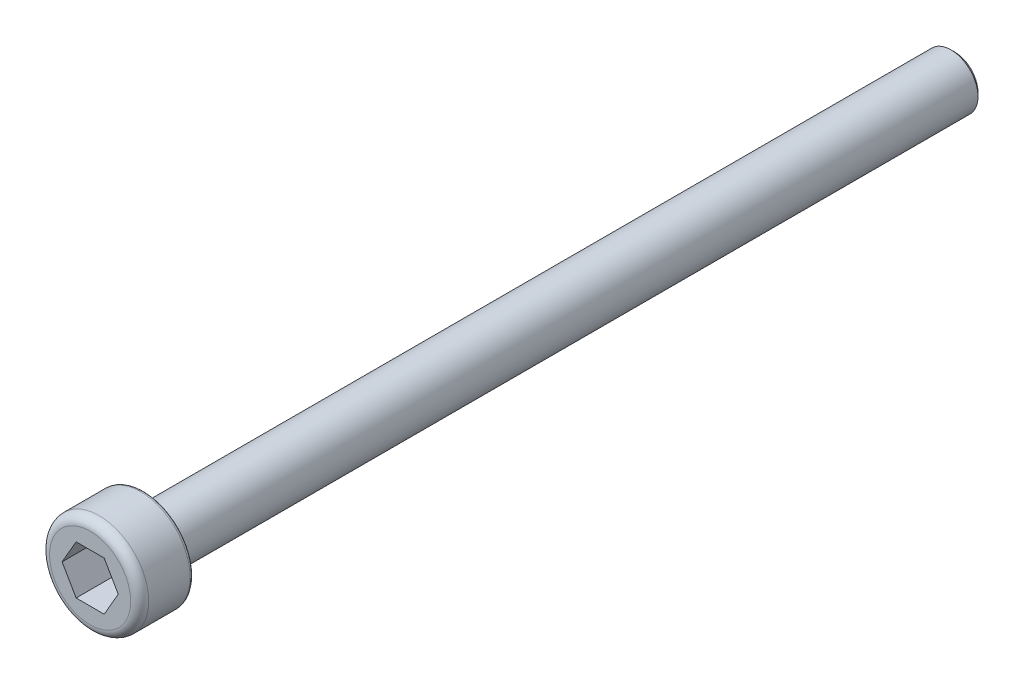
SolidWorks part; units mm, degrees
ref_plane "前视" through (0, 0, 0) normal (0, 0, 1) x (1, 0, 0)
ref_plane "上视" through (0, 0, 0) normal (0, 1, 0) x (1, 0, 0)
ref_plane "右视" through (0, 0, 0) normal (1, 0, 0) x (0, 0, -1)
sketch "草图1" plane through (0, 0, 0) normal (0, 0, 1) x (1, 0, 0)
  circle A0 centre (0, 0) radius 2.75
  dimension "D1" = 5.5
extrude "凸台-拉伸1" add sketch "草图1" along normal blind 3
fillet "圆角1" radius 0.5 1 edges at (2.75, 0, 3)
sketch "草图2" plane through (0, 0, 3) normal (0, 0, 1) x (1, 0, 0)
  line L1 (1.5588, 0) -> (0.7794, 1.35)
  line L2 (0.7794, 1.35) -> (-0.7794, 1.35)
  line L3 (-0.7794, 1.35) -> (-1.5588, 0)
  line L4 (-1.5588, 0) -> (-0.7794, -1.35)
  line L5 (-0.7794, -1.35) -> (0.7794, -1.35)
  line L6 (0.7794, -1.35) -> (1.5588, 0)
  circle A0 centre (0, 0) radius 1.35 construction
  dimension "D1" = 2.7
extrude "切除-拉伸1" cut sketch "草图2" against normal blind 2
sketch "草图3" plane through (0, 0, 0) normal (0, 0, -1) x (-1, 0, 0)
  circle A0 centre (0, 0) radius 1.5
  dimension "D1" = 3
extrude "凸台-拉伸2" add sketch "草图3" along normal blind 45
chamfer "倒角1" distance 0.2 angle 45 1 edges at (-1.5, 0, -45)
fillet "圆角2" radius 0.2 1 edges at (2.75, 0, 0)
